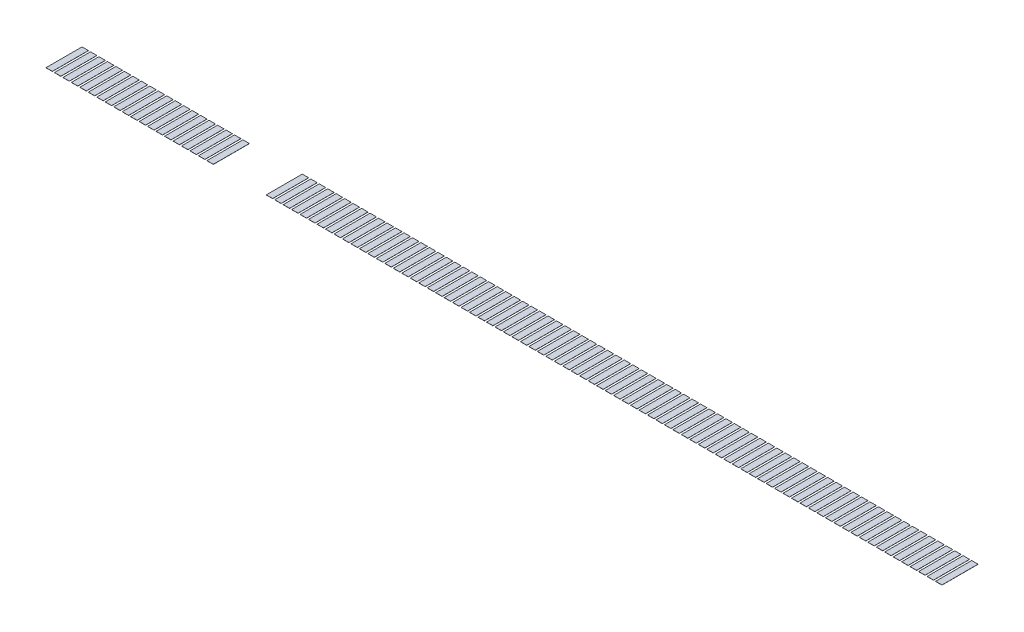
SolidWorks part; units mm, degrees
material "铜"
ref_plane "Front" through (0, 0, 0) normal (0, 0, 1) x (1, 0, 0)
ref_plane "Top" through (0, 0, 0) normal (0, 1, 0) x (1, 0, 0)
ref_plane "Right" through (0, 0, 0) normal (1, 0, 0) x (0, 0, -1)
sketch "草图1" plane through (0, 0, 0) normal (0, 1, 0) x (1, 0, 0)
  line L0 (0.375, -1.275) -> (0.825, -1.275)
  line L1 (-0.225, 1.275) -> (0.225, 1.275)
  line L2 (-0.225, 1.275) -> (-0.225, -1.275)
  line L3 (-0.225, -1.275) -> (0.225, -1.275)
  line L4 (0.225, 1.275) -> (0.225, -1.275)
  line L5 (-0.225, 1.275) -> (0.225, -1.275) construction
  line L6 (-0.225, -1.275) -> (0.225, 1.275) construction
  line L7 (0.825, 1.275) -> (0.825, -1.275)
  line L8 (0.375, 1.275) -> (0.375, -1.275)
  line L9 (0.375, 1.275) -> (0.825, 1.275)
  line L10 (0.975, -1.275) -> (1.425, -1.275)
  line L11 (1.425, 1.275) -> (1.425, -1.275)
  line L12 (0.975, 1.275) -> (0.975, -1.275)
  line L13 (0.975, 1.275) -> (1.425, 1.275)
  line L14 (1.575, -1.275) -> (2.025, -1.275)
  line L15 (2.025, 1.275) -> (2.025, -1.275)
  line L16 (1.575, 1.275) -> (1.575, -1.275)
  line L17 (1.575, 1.275) -> (2.025, 1.275)
  line L18 (2.175, -1.275) -> (2.625, -1.275)
  line L19 (2.625, 1.275) -> (2.625, -1.275)
  line L20 (2.175, 1.275) -> (2.175, -1.275)
  line L21 (2.175, 1.275) -> (2.625, 1.275)
  line L22 (2.775, -1.275) -> (3.225, -1.275)
  line L23 (3.225, 1.275) -> (3.225, -1.275)
  line L24 (2.775, 1.275) -> (2.775, -1.275)
  line L25 (2.775, 1.275) -> (3.225, 1.275)
  line L26 (3.375, -1.275) -> (3.825, -1.275)
  line L27 (3.825, 1.275) -> (3.825, -1.275)
  line L28 (3.375, 1.275) -> (3.375, -1.275)
  line L29 (3.375, 1.275) -> (3.825, 1.275)
  line L30 (3.975, -1.275) -> (4.425, -1.275)
  line L31 (4.425, 1.275) -> (4.425, -1.275)
  line L32 (3.975, 1.275) -> (3.975, -1.275)
  line L33 (3.975, 1.275) -> (4.425, 1.275)
  line L34 (4.575, -1.275) -> (5.025, -1.275)
  line L35 (5.025, 1.275) -> (5.025, -1.275)
  line L36 (4.575, 1.275) -> (4.575, -1.275)
  line L37 (4.575, 1.275) -> (5.025, 1.275)
  line L38 (5.175, -1.275) -> (5.625, -1.275)
  line L39 (5.625, 1.275) -> (5.625, -1.275)
  line L40 (5.175, 1.275) -> (5.175, -1.275)
  line L41 (5.175, 1.275) -> (5.625, 1.275)
  line L42 (5.775, -1.275) -> (6.225, -1.275)
  line L43 (6.225, 1.275) -> (6.225, -1.275)
  line L44 (5.775, 1.275) -> (5.775, -1.275)
  line L45 (5.775, 1.275) -> (6.225, 1.275)
  line L46 (6.375, -1.275) -> (6.825, -1.275)
  line L47 (6.825, 1.275) -> (6.825, -1.275)
  line L48 (6.375, 1.275) -> (6.375, -1.275)
  line L49 (6.375, 1.275) -> (6.825, 1.275)
  line L50 (6.975, -1.275) -> (7.425, -1.275)
  line L51 (7.425, 1.275) -> (7.425, -1.275)
  line L52 (6.975, 1.275) -> (6.975, -1.275)
  line L53 (6.975, 1.275) -> (7.425, 1.275)
  line L54 (7.575, -1.275) -> (8.025, -1.275)
  line L55 (8.025, 1.275) -> (8.025, -1.275)
  line L56 (7.575, 1.275) -> (7.575, -1.275)
  line L57 (7.575, 1.275) -> (8.025, 1.275)
  line L58 (8.175, -1.275) -> (8.625, -1.275)
  line L59 (8.625, 1.275) -> (8.625, -1.275)
  line L60 (8.175, 1.275) -> (8.175, -1.275)
  line L61 (8.175, 1.275) -> (8.625, 1.275)
  line L62 (8.775, -1.275) -> (9.225, -1.275)
  line L63 (9.225, 1.275) -> (9.225, -1.275)
  line L64 (8.775, 1.275) -> (8.775, -1.275)
  line L65 (8.775, 1.275) -> (9.225, 1.275)
  line L66 (9.375, -1.275) -> (9.825, -1.275)
  line L67 (9.825, 1.275) -> (9.825, -1.275)
  line L68 (9.375, 1.275) -> (9.375, -1.275)
  line L69 (9.375, 1.275) -> (9.825, 1.275)
  line L70 (9.975, -1.275) -> (10.425, -1.275)
  line L71 (10.425, 1.275) -> (10.425, -1.275)
  line L72 (9.975, 1.275) -> (9.975, -1.275)
  line L73 (9.975, 1.275) -> (10.425, 1.275)
  line L74 (10.575, -1.275) -> (11.025, -1.275)
  line L75 (11.025, 1.275) -> (11.025, -1.275)
  line L76 (10.575, 1.275) -> (10.575, -1.275)
  line L77 (10.575, 1.275) -> (11.025, 1.275)
  line L78 (11.175, -1.275) -> (11.625, -1.275)
  line L79 (11.625, 1.275) -> (11.625, -1.275)
  line L80 (11.175, 1.275) -> (11.175, -1.275)
  line L81 (11.175, 1.275) -> (11.625, 1.275)
  line L106 (15.375, -1.275) -> (15.825, -1.275)
  line L107 (15.825, 1.275) -> (15.825, -1.275)
  line L108 (15.375, 1.275) -> (15.375, -1.275)
  line L109 (15.375, 1.275) -> (15.825, 1.275)
  line L110 (15.975, -1.275) -> (16.425, -1.275)
  line L111 (16.425, 1.275) -> (16.425, -1.275)
  line L112 (15.975, 1.275) -> (15.975, -1.275)
  line L113 (15.975, 1.275) -> (16.425, 1.275)
  line L114 (16.575, -1.275) -> (17.025, -1.275)
  line L115 (17.025, 1.275) -> (17.025, -1.275)
  line L116 (16.575, 1.275) -> (16.575, -1.275)
  line L117 (16.575, 1.275) -> (17.025, 1.275)
  line L118 (17.175, -1.275) -> (17.625, -1.275)
  line L119 (17.625, 1.275) -> (17.625, -1.275)
  line L120 (17.175, 1.275) -> (17.175, -1.275)
  line L121 (17.175, 1.275) -> (17.625, 1.275)
  line L122 (17.775, -1.275) -> (18.225, -1.275)
  line L123 (18.225, 1.275) -> (18.225, -1.275)
  line L124 (17.775, 1.275) -> (17.775, -1.275)
  line L125 (17.775, 1.275) -> (18.225, 1.275)
  line L126 (18.375, -1.275) -> (18.825, -1.275)
  line L127 (18.825, 1.275) -> (18.825, -1.275)
  line L128 (18.375, 1.275) -> (18.375, -1.275)
  line L129 (18.375, 1.275) -> (18.825, 1.275)
  line L130 (18.975, -1.275) -> (19.425, -1.275)
  line L131 (19.425, 1.275) -> (19.425, -1.275)
  line L132 (18.975, 1.275) -> (18.975, -1.275)
  line L133 (18.975, 1.275) -> (19.425, 1.275)
  line L134 (19.575, -1.275) -> (20.025, -1.275)
  line L135 (20.025, 1.275) -> (20.025, -1.275)
  line L136 (19.575, 1.275) -> (19.575, -1.275)
  line L137 (19.575, 1.275) -> (20.025, 1.275)
  line L138 (20.175, -1.275) -> (20.625, -1.275)
  line L139 (20.625, 1.275) -> (20.625, -1.275)
  line L140 (20.175, 1.275) -> (20.175, -1.275)
  line L141 (20.175, 1.275) -> (20.625, 1.275)
  line L142 (20.775, -1.275) -> (21.225, -1.275)
  line L143 (21.225, 1.275) -> (21.225, -1.275)
  line L144 (20.775, 1.275) -> (20.775, -1.275)
  line L145 (20.775, 1.275) -> (21.225, 1.275)
  line L146 (21.375, -1.275) -> (21.825, -1.275)
  line L147 (21.825, 1.275) -> (21.825, -1.275)
  line L148 (21.375, 1.275) -> (21.375, -1.275)
  line L149 (21.375, 1.275) -> (21.825, 1.275)
  line L150 (21.975, -1.275) -> (22.425, -1.275)
  line L151 (22.425, 1.275) -> (22.425, -1.275)
  line L152 (21.975, 1.275) -> (21.975, -1.275)
  line L153 (21.975, 1.275) -> (22.425, 1.275)
  line L154 (22.575, -1.275) -> (23.025, -1.275)
  line L155 (23.025, 1.275) -> (23.025, -1.275)
  line L156 (22.575, 1.275) -> (22.575, -1.275)
  line L157 (22.575, 1.275) -> (23.025, 1.275)
  line L158 (23.175, -1.275) -> (23.625, -1.275)
  line L159 (23.625, 1.275) -> (23.625, -1.275)
  line L160 (23.175, 1.275) -> (23.175, -1.275)
  line L161 (23.175, 1.275) -> (23.625, 1.275)
  line L162 (23.775, -1.275) -> (24.225, -1.275)
  line L163 (24.225, 1.275) -> (24.225, -1.275)
  line L164 (23.775, 1.275) -> (23.775, -1.275)
  line L165 (23.775, 1.275) -> (24.225, 1.275)
  line L166 (24.375, -1.275) -> (24.825, -1.275)
  line L167 (24.825, 1.275) -> (24.825, -1.275)
  line L168 (24.375, 1.275) -> (24.375, -1.275)
  line L169 (24.375, 1.275) -> (24.825, 1.275)
  line L170 (24.975, -1.275) -> (25.425, -1.275)
  line L171 (25.425, 1.275) -> (25.425, -1.275)
  line L172 (24.975, 1.275) -> (24.975, -1.275)
  line L173 (24.975, 1.275) -> (25.425, 1.275)
  line L174 (25.575, -1.275) -> (26.025, -1.275)
  line L175 (26.025, 1.275) -> (26.025, -1.275)
  line L176 (25.575, 1.275) -> (25.575, -1.275)
  line L177 (25.575, 1.275) -> (26.025, 1.275)
  line L178 (26.175, -1.275) -> (26.625, -1.275)
  line L179 (26.625, 1.275) -> (26.625, -1.275)
  line L180 (26.175, 1.275) -> (26.175, -1.275)
  line L181 (26.175, 1.275) -> (26.625, 1.275)
  line L182 (26.775, -1.275) -> (27.225, -1.275)
  line L183 (27.225, 1.275) -> (27.225, -1.275)
  line L184 (26.775, 1.275) -> (26.775, -1.275)
  line L185 (26.775, 1.275) -> (27.225, 1.275)
  line L186 (27.375, -1.275) -> (27.825, -1.275)
  line L187 (27.825, 1.275) -> (27.825, -1.275)
  line L188 (27.375, 1.275) -> (27.375, -1.275)
  line L189 (27.375, 1.275) -> (27.825, 1.275)
  line L190 (27.975, -1.275) -> (28.425, -1.275)
  line L191 (28.425, 1.275) -> (28.425, -1.275)
  line L192 (27.975, 1.275) -> (27.975, -1.275)
  line L193 (27.975, 1.275) -> (28.425, 1.275)
  line L194 (28.575, -1.275) -> (29.025, -1.275)
  line L195 (29.025, 1.275) -> (29.025, -1.275)
  line L196 (28.575, 1.275) -> (28.575, -1.275)
  line L197 (28.575, 1.275) -> (29.025, 1.275)
  line L198 (29.175, -1.275) -> (29.625, -1.275)
  line L199 (29.625, 1.275) -> (29.625, -1.275)
  line L200 (29.175, 1.275) -> (29.175, -1.275)
  line L201 (29.175, 1.275) -> (29.625, 1.275)
  line L202 (29.775, -1.275) -> (30.225, -1.275)
  line L203 (30.225, 1.275) -> (30.225, -1.275)
  line L204 (29.775, 1.275) -> (29.775, -1.275)
  line L205 (29.775, 1.275) -> (30.225, 1.275)
  line L206 (30.375, -1.275) -> (30.825, -1.275)
  line L207 (30.825, 1.275) -> (30.825, -1.275)
  line L208 (30.375, 1.275) -> (30.375, -1.275)
  line L209 (30.375, 1.275) -> (30.825, 1.275)
  line L210 (30.975, -1.275) -> (31.425, -1.275)
  line L211 (31.425, 1.275) -> (31.425, -1.275)
  line L212 (30.975, 1.275) -> (30.975, -1.275)
  line L213 (30.975, 1.275) -> (31.425, 1.275)
  line L214 (31.575, -1.275) -> (32.025, -1.275)
  line L215 (32.025, 1.275) -> (32.025, -1.275)
  line L216 (31.575, 1.275) -> (31.575, -1.275)
  line L217 (31.575, 1.275) -> (32.025, 1.275)
  line L218 (32.175, -1.275) -> (32.625, -1.275)
  line L219 (32.625, 1.275) -> (32.625, -1.275)
  line L220 (32.175, 1.275) -> (32.175, -1.275)
  line L221 (32.175, 1.275) -> (32.625, 1.275)
  line L222 (32.775, -1.275) -> (33.225, -1.275)
  line L223 (33.225, 1.275) -> (33.225, -1.275)
  line L224 (32.775, 1.275) -> (32.775, -1.275)
  line L225 (32.775, 1.275) -> (33.225, 1.275)
  line L226 (33.375, -1.275) -> (33.825, -1.275)
  line L227 (33.825, 1.275) -> (33.825, -1.275)
  line L228 (33.375, 1.275) -> (33.375, -1.275)
  line L229 (33.375, 1.275) -> (33.825, 1.275)
  line L230 (33.975, -1.275) -> (34.425, -1.275)
  line L231 (34.425, 1.275) -> (34.425, -1.275)
  line L232 (33.975, 1.275) -> (33.975, -1.275)
  line L233 (33.975, 1.275) -> (34.425, 1.275)
  line L234 (34.575, -1.275) -> (35.025, -1.275)
  line L235 (35.025, 1.275) -> (35.025, -1.275)
  line L236 (34.575, 1.275) -> (34.575, -1.275)
  line L237 (34.575, 1.275) -> (35.025, 1.275)
  line L238 (35.175, -1.275) -> (35.625, -1.275)
  line L239 (35.625, 1.275) -> (35.625, -1.275)
  line L240 (35.175, 1.275) -> (35.175, -1.275)
  line L241 (35.175, 1.275) -> (35.625, 1.275)
  line L242 (35.775, -1.275) -> (36.225, -1.275)
  line L243 (36.225, 1.275) -> (36.225, -1.275)
  line L244 (35.775, 1.275) -> (35.775, -1.275)
  line L245 (35.775, 1.275) -> (36.225, 1.275)
  line L246 (36.375, -1.275) -> (36.825, -1.275)
  line L247 (36.825, 1.275) -> (36.825, -1.275)
  line L248 (36.375, 1.275) -> (36.375, -1.275)
  line L249 (36.375, 1.275) -> (36.825, 1.275)
  line L250 (36.975, -1.275) -> (37.425, -1.275)
  line L251 (37.425, 1.275) -> (37.425, -1.275)
  line L252 (36.975, 1.275) -> (36.975, -1.275)
  line L253 (36.975, 1.275) -> (37.425, 1.275)
  line L254 (37.575, -1.275) -> (38.025, -1.275)
  line L255 (38.025, 1.275) -> (38.025, -1.275)
  line L256 (37.575, 1.275) -> (37.575, -1.275)
  line L257 (37.575, 1.275) -> (38.025, 1.275)
  line L258 (38.175, -1.275) -> (38.625, -1.275)
  line L259 (38.625, 1.275) -> (38.625, -1.275)
  line L260 (38.175, 1.275) -> (38.175, -1.275)
  line L261 (38.175, 1.275) -> (38.625, 1.275)
  line L262 (38.775, -1.275) -> (39.225, -1.275)
  line L263 (39.225, 1.275) -> (39.225, -1.275)
  line L264 (38.775, 1.275) -> (38.775, -1.275)
  line L265 (38.775, 1.275) -> (39.225, 1.275)
  line L266 (39.375, -1.275) -> (39.825, -1.275)
  line L267 (39.825, 1.275) -> (39.825, -1.275)
  line L268 (39.375, 1.275) -> (39.375, -1.275)
  line L269 (39.375, 1.275) -> (39.825, 1.275)
  line L270 (39.975, -1.275) -> (40.425, -1.275)
  line L271 (40.425, 1.275) -> (40.425, -1.275)
  line L272 (39.975, 1.275) -> (39.975, -1.275)
  line L273 (39.975, 1.275) -> (40.425, 1.275)
  line L274 (40.575, -1.275) -> (41.025, -1.275)
  line L275 (41.025, 1.275) -> (41.025, -1.275)
  line L276 (40.575, 1.275) -> (40.575, -1.275)
  line L277 (40.575, 1.275) -> (41.025, 1.275)
  line L278 (41.175, -1.275) -> (41.625, -1.275)
  line L279 (41.625, 1.275) -> (41.625, -1.275)
  line L280 (41.175, 1.275) -> (41.175, -1.275)
  line L281 (41.175, 1.275) -> (41.625, 1.275)
  line L282 (41.775, -1.275) -> (42.225, -1.275)
  line L283 (42.225, 1.275) -> (42.225, -1.275)
  line L284 (41.775, 1.275) -> (41.775, -1.275)
  line L285 (41.775, 1.275) -> (42.225, 1.275)
  line L286 (42.375, -1.275) -> (42.825, -1.275)
  line L287 (42.825, 1.275) -> (42.825, -1.275)
  line L288 (42.375, 1.275) -> (42.375, -1.275)
  line L289 (42.375, 1.275) -> (42.825, 1.275)
  line L290 (42.975, -1.275) -> (43.425, -1.275)
  line L291 (43.425, 1.275) -> (43.425, -1.275)
  line L292 (42.975, 1.275) -> (42.975, -1.275)
  line L293 (42.975, 1.275) -> (43.425, 1.275)
  line L294 (43.575, -1.275) -> (44.025, -1.275)
  line L295 (44.025, 1.275) -> (44.025, -1.275)
  line L296 (43.575, 1.275) -> (43.575, -1.275)
  line L297 (43.575, 1.275) -> (44.025, 1.275)
  line L298 (44.175, -1.275) -> (44.625, -1.275)
  line L299 (44.625, 1.275) -> (44.625, -1.275)
  line L300 (44.175, 1.275) -> (44.175, -1.275)
  line L301 (44.175, 1.275) -> (44.625, 1.275)
  line L302 (44.775, -1.275) -> (45.225, -1.275)
  line L303 (45.225, 1.275) -> (45.225, -1.275)
  line L304 (44.775, 1.275) -> (44.775, -1.275)
  line L305 (44.775, 1.275) -> (45.225, 1.275)
  line L306 (45.375, -1.275) -> (45.825, -1.275)
  line L307 (45.825, 1.275) -> (45.825, -1.275)
  line L308 (45.375, 1.275) -> (45.375, -1.275)
  line L309 (45.375, 1.275) -> (45.825, 1.275)
  line L310 (45.975, -1.275) -> (46.425, -1.275)
  line L311 (46.425, 1.275) -> (46.425, -1.275)
  line L312 (45.975, 1.275) -> (45.975, -1.275)
  line L313 (45.975, 1.275) -> (46.425, 1.275)
  line L314 (46.575, -1.275) -> (47.025, -1.275)
  line L315 (47.025, 1.275) -> (47.025, -1.275)
  line L316 (46.575, 1.275) -> (46.575, -1.275)
  line L317 (46.575, 1.275) -> (47.025, 1.275)
  line L318 (47.175, -1.275) -> (47.625, -1.275)
  line L319 (47.625, 1.275) -> (47.625, -1.275)
  line L320 (47.175, 1.275) -> (47.175, -1.275)
  line L321 (47.175, 1.275) -> (47.625, 1.275)
  line L322 (47.775, -1.275) -> (48.225, -1.275)
  line L323 (48.225, 1.275) -> (48.225, -1.275)
  line L324 (47.775, 1.275) -> (47.775, -1.275)
  line L325 (47.775, 1.275) -> (48.225, 1.275)
  line L326 (48.375, -1.275) -> (48.825, -1.275)
  line L327 (48.825, 1.275) -> (48.825, -1.275)
  line L328 (48.375, 1.275) -> (48.375, -1.275)
  line L329 (48.375, 1.275) -> (48.825, 1.275)
  line L330 (48.975, -1.275) -> (49.425, -1.275)
  line L331 (49.425, 1.275) -> (49.425, -1.275)
  line L332 (48.975, 1.275) -> (48.975, -1.275)
  line L333 (48.975, 1.275) -> (49.425, 1.275)
  line L334 (49.575, -1.275) -> (50.025, -1.275)
  line L335 (50.025, 1.275) -> (50.025, -1.275)
  line L336 (49.575, 1.275) -> (49.575, -1.275)
  line L337 (49.575, 1.275) -> (50.025, 1.275)
  line L338 (50.175, -1.275) -> (50.625, -1.275)
  line L339 (50.625, 1.275) -> (50.625, -1.275)
  line L340 (50.175, 1.275) -> (50.175, -1.275)
  line L341 (50.175, 1.275) -> (50.625, 1.275)
  line L342 (50.775, -1.275) -> (51.225, -1.275)
  line L343 (51.225, 1.275) -> (51.225, -1.275)
  line L344 (50.775, 1.275) -> (50.775, -1.275)
  line L345 (50.775, 1.275) -> (51.225, 1.275)
  line L346 (51.375, -1.275) -> (51.825, -1.275)
  line L347 (51.825, 1.275) -> (51.825, -1.275)
  line L348 (51.375, 1.275) -> (51.375, -1.275)
  line L349 (51.375, 1.275) -> (51.825, 1.275)
  line L350 (51.975, -1.275) -> (52.425, -1.275)
  line L351 (52.425, 1.275) -> (52.425, -1.275)
  line L352 (51.975, 1.275) -> (51.975, -1.275)
  line L353 (51.975, 1.275) -> (52.425, 1.275)
  line L354 (52.575, -1.275) -> (53.025, -1.275)
  line L355 (53.025, 1.275) -> (53.025, -1.275)
  line L356 (52.575, 1.275) -> (52.575, -1.275)
  line L357 (52.575, 1.275) -> (53.025, 1.275)
  line L358 (53.175, -1.275) -> (53.625, -1.275)
  line L359 (53.625, 1.275) -> (53.625, -1.275)
  line L360 (53.175, 1.275) -> (53.175, -1.275)
  line L361 (53.175, 1.275) -> (53.625, 1.275)
  line L362 (53.775, -1.275) -> (54.225, -1.275)
  line L363 (54.225, 1.275) -> (54.225, -1.275)
  line L364 (53.775, 1.275) -> (53.775, -1.275)
  line L365 (53.775, 1.275) -> (54.225, 1.275)
  line L366 (54.375, -1.275) -> (54.825, -1.275)
  line L367 (54.825, 1.275) -> (54.825, -1.275)
  line L368 (54.375, 1.275) -> (54.375, -1.275)
  line L369 (54.375, 1.275) -> (54.825, 1.275)
  line L370 (54.975, -1.275) -> (55.425, -1.275)
  line L371 (55.425, 1.275) -> (55.425, -1.275)
  line L372 (54.975, 1.275) -> (54.975, -1.275)
  line L373 (54.975, 1.275) -> (55.425, 1.275)
  line L374 (55.575, -1.275) -> (56.025, -1.275)
  line L375 (56.025, 1.275) -> (56.025, -1.275)
  line L376 (55.575, 1.275) -> (55.575, -1.275)
  line L377 (55.575, 1.275) -> (56.025, 1.275)
  line L378 (56.175, -1.275) -> (56.625, -1.275)
  line L379 (56.625, 1.275) -> (56.625, -1.275)
  line L380 (56.175, 1.275) -> (56.175, -1.275)
  line L381 (56.175, 1.275) -> (56.625, 1.275)
  line L382 (56.775, -1.275) -> (57.225, -1.275)
  line L383 (57.225, 1.275) -> (57.225, -1.275)
  line L384 (56.775, 1.275) -> (56.775, -1.275)
  line L385 (56.775, 1.275) -> (57.225, 1.275)
  line L386 (57.375, -1.275) -> (57.825, -1.275)
  line L387 (57.825, 1.275) -> (57.825, -1.275)
  line L388 (57.375, 1.275) -> (57.375, -1.275)
  line L389 (57.375, 1.275) -> (57.825, 1.275)
  line L390 (57.975, -1.275) -> (58.425, -1.275)
  line L391 (58.425, 1.275) -> (58.425, -1.275)
  line L392 (57.975, 1.275) -> (57.975, -1.275)
  line L393 (57.975, 1.275) -> (58.425, 1.275)
  line L394 (58.575, -1.275) -> (59.025, -1.275)
  line L395 (59.025, 1.275) -> (59.025, -1.275)
  line L396 (58.575, 1.275) -> (58.575, -1.275)
  line L397 (58.575, 1.275) -> (59.025, 1.275)
  line L398 (59.175, -1.275) -> (59.625, -1.275)
  line L399 (59.625, 1.275) -> (59.625, -1.275)
  line L400 (59.175, 1.275) -> (59.175, -1.275)
  line L401 (59.175, 1.275) -> (59.625, 1.275)
  line L402 (59.775, -1.275) -> (60.225, -1.275)
  line L403 (60.225, 1.275) -> (60.225, -1.275)
  line L404 (59.775, 1.275) -> (59.775, -1.275)
  line L405 (59.775, 1.275) -> (60.225, 1.275)
  line L406 (60.375, -1.275) -> (60.825, -1.275)
  line L407 (60.825, 1.275) -> (60.825, -1.275)
  line L408 (60.375, 1.275) -> (60.375, -1.275)
  line L409 (60.375, 1.275) -> (60.825, 1.275)
  line L410 (60.975, -1.275) -> (61.425, -1.275)
  line L411 (61.425, 1.275) -> (61.425, -1.275)
  line L412 (60.975, 1.275) -> (60.975, -1.275)
  line L413 (60.975, 1.275) -> (61.425, 1.275)
  line L414 (61.575, -1.275) -> (62.025, -1.275)
  line L415 (62.025, 1.275) -> (62.025, -1.275)
  line L416 (61.575, 1.275) -> (61.575, -1.275)
  line L417 (61.575, 1.275) -> (62.025, 1.275)
  line L418 (62.175, -1.275) -> (62.625, -1.275)
  line L419 (62.625, 1.275) -> (62.625, -1.275)
  line L420 (62.175, 1.275) -> (62.175, -1.275)
  line L421 (62.175, 1.275) -> (62.625, 1.275)
  line L422 (62.775, -1.275) -> (63.225, -1.275)
  line L423 (63.225, 1.275) -> (63.225, -1.275)
  line L424 (62.775, 1.275) -> (62.775, -1.275)
  line L425 (62.775, 1.275) -> (63.225, 1.275)
  line L798 (11.775, 1.275) -> (12.225, 1.275) [skipped]
  line L799 (12.225, 1.275) -> (12.225, -1.275) [skipped]
  line L800 (11.775, 1.275) -> (11.775, -1.275) [skipped]
  line L801 (11.775, -1.275) -> (12.225, -1.275) [skipped]
  line L802 (12.375, -1.275) -> (12.825, -1.275) [skipped]
  line L803 (12.825, 1.275) -> (12.825, -1.275) [skipped]
  line L804 (12.375, 1.275) -> (12.375, -1.275) [skipped]
  line L805 (12.375, 1.275) -> (12.825, 1.275) [skipped]
  line L806 (12.975, -1.275) -> (13.425, -1.275) [skipped]
  line L807 (13.425, 1.275) -> (13.425, -1.275) [skipped]
  line L808 (12.975, 1.275) -> (12.975, -1.275) [skipped]
  line L809 (12.975, 1.275) -> (13.425, 1.275) [skipped]
  line L810 (13.575, -1.275) -> (14.025, -1.275) [skipped]
  line L811 (14.025, 1.275) -> (14.025, -1.275) [skipped]
  line L812 (13.575, 1.275) -> (13.575, -1.275) [skipped]
  line L813 (13.575, 1.275) -> (14.025, 1.275) [skipped]
  line L814 (14.175, -1.275) -> (14.625, -1.275) [skipped]
  line L815 (14.625, 1.275) -> (14.625, -1.275) [skipped]
  line L816 (14.175, 1.275) -> (14.175, -1.275) [skipped]
  line L817 (14.175, 1.275) -> (14.625, 1.275) [skipped]
  line L818 (14.775, -1.275) -> (15.225, -1.275) [skipped]
  line L819 (15.225, 1.275) -> (15.225, -1.275) [skipped]
  line L820 (14.775, 1.275) -> (14.775, -1.275) [skipped]
  line L821 (14.775, 1.275) -> (15.225, 1.275) [skipped]
  point P0 (0, 0)
  point P6 (0, 0)
  dimension "D1" = 2.55
  dimension "D2" = 0.45
  dimension "D3" = 106
extrude "凸台-拉伸2" add sketch "草图1" against normal blind 0.01
